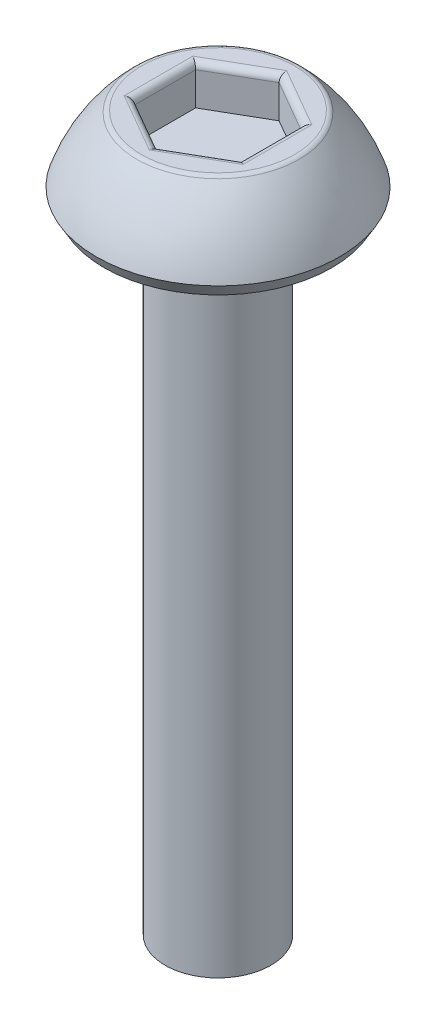
SolidWorks part; units mm, degrees
ref_plane "Front Plane" through (0, 0, 0) normal (0, 0, 1) x (1, 0, 0)
ref_plane "Top Plane" through (0, 0, 0) normal (0, 1, 0) x (1, 0, 0)
ref_plane "Right Plane" through (0, 0, 0) normal (1, 0, 0) x (0, 0, -1)
sketch "Sketch1" plane through (0, 0, 0) normal (1, 0, 0) x (0, 0, -1)
  line L0 (0, 0) -> (0, 1.5) construction
  line L1 (0, 1.5) -> (-1.5, 1.5)
  line L3 (-2.3, 0.25) -> (-2.1557, 0)
  line L4 (-2.1557, 0) -> (-1, 0)
  line L5 (-1, 0) -> (-1, -12)
  line L6 (-1, -12) -> (0, -12)
  line L7 (0, -12) -> (0, 1.5)
  line L8 (0, 0) -> (-1, 0) construction
  arc A0 (-1.5, 1.5) -> (-2.3, 0.25) centre (0.5483, -0.6919) ccw
  dimension "D5" = 3
  dimension "D1" = 1.5
  dimension "D2" = 2.3
  dimension "D3" = 1.5
  dimension "D4" = 0.25
  dimension "D6" = 60
  dimension "D7" = 1
  dimension "D8" = 12
  dimension "D9" = 2.3
revolve "Revolve1" add sketch "Sketch1" angle 360 about L7
sketch "Sketch2" plane through (0, 1.5, 0) normal (0, 1, 0) x (1, 0, 0)
  line L1 (0, 1.1547) -> (-1, 0.5774)
  line L2 (-1, 0.5774) -> (-1, -0.5774)
  line L3 (-1, -0.5774) -> (0, -1.1547)
  line L4 (0, -1.1547) -> (1, -0.5774)
  line L5 (1, -0.5774) -> (1, 0.5774)
  line L6 (1, 0.5774) -> (0, 1.1547)
  circle A0 centre (0, 0) radius 1 construction
  dimension "D1" = 2
extrude "Cut-Extrude1" cut sketch "Sketch2" against normal blind 0.75
fillet "Fillet1" radius 0.125 7 edges at (0, 1.5, -1.5) (-0.5, 1.5, 0.866) (0.5, 1.5, 0.866) (1, 1.5, 0) (0.5, 1.5, -0.866) (-0.5, 1.5, -0.866) (-1, 1.5, 0)
